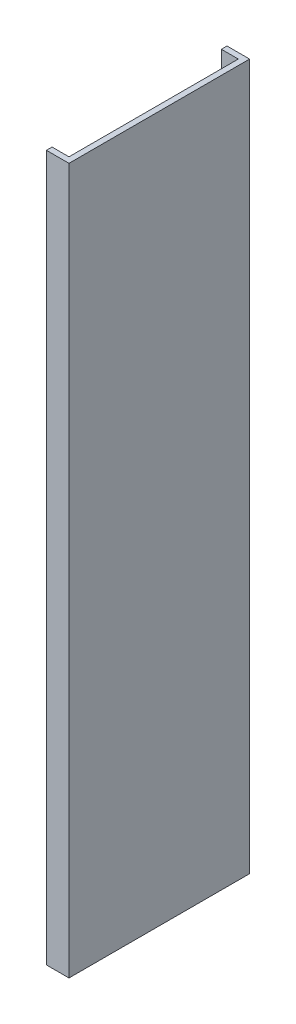
SolidWorks part; units mm, degrees
material "201 Annealed Stainless Steel (SS)"
ref_plane "Front Plane" through (0, 0, 0) normal (0, 0, 1) x (1, 0, 0)
ref_plane "Top Plane" through (0, 0, 0) normal (0, 1, 0) x (1, 0, 0)
ref_plane "Right Plane" through (0, 0, 0) normal (1, 0, 0) x (0, 0, -1)
sketch "Sketch1" plane through (0, 0, 0) normal (0, 1, 0) x (1, 0, 0)
  line L0 (-15, 75) -> (0, 75)
  line L1 (0, 75) -> (0, -75)
  line L2 (0, -75) -> (-15, -75)
  dimension "D1" = 150
  dimension "D2" = 15
extrude "Extrude-Thin1" add sketch "Sketch1" along normal blind 625 thin thin type one direction reverse wall 5
